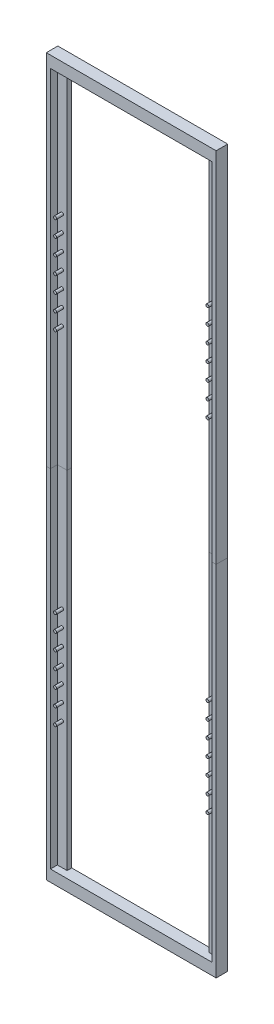
SolidWorks part; units mm, degrees
ref_plane "Front Plane" through (0, 0, 0) normal (1, 0, 0) x (0, 1, 0)
ref_plane "Top Plane" through (0, 0, 0) normal (0, 0, 1) x (0, 1, 0)
ref_plane "Right Plane" through (0, 0, 0) normal (0, 1, 0) x (-1, 0, 0)
sketch "Sketch1" plane through (0, 0, 0) normal (0, 0, 1) x (0, 1, 0)
  line L1 (-150, -30.75) -> (150, -30.75)
  line L2 (-150, -30.75) -> (-150, 30.75)
  line L3 (-150, 30.75) -> (150, 30.75)
  line L4 (150, -30.75) -> (150, 30.75)
  line L5 (-150, -30.75) -> (150, 30.75) construction
  line L6 (-150, 30.75) -> (150, -30.75) construction
  line L7 (-155, -36.75) -> (155, -36.75)
  line L8 (-155, -36.75) -> (-155, 36.75)
  line L9 (-155, 36.75) -> (155, 36.75)
  line L10 (155, -36.75) -> (155, 36.75)
  line L11 (-155, -36.75) -> (155, 36.75) construction
  line L12 (-155, 36.75) -> (155, -36.75) construction
  point P0 (0, 0)
  point P6 (0, 0)
  dimension "D1" = 61.5
  dimension "D2" = 6
  dimension "D3" = 300
  dimension "D4" = 310
extrude "Boss-Extrude1" add sketch "Sketch1" along normal blind 5
sketch "Sketch2" plane through (0, 0, 5) normal (0, 0, 1) x (1, 0, 0)
  line L1 (-30.75, 150) -> (-34.95, 150)
  line L2 (-30.75, 150) -> (-30.75, -150)
  line L3 (-30.75, -150) -> (-34.95, -150)
  line L4 (-34.95, 150) -> (-34.95, -150)
  line L5 (30.75, -150) -> (34.95, -150)
  line L6 (30.75, -150) -> (30.75, 150)
  line L7 (30.75, 150) -> (34.95, 150)
  line L8 (34.95, -150) -> (34.95, 150)
  dimension "D1" = 4.2
  dimension "D2" = 4.2
ref_plane "Plane1" through (-36.75, 155, 5) normal (0, -1, 0) x (-1, 0, 0)
extrude "Cut-Extrude1" cut sketch "Sketch2" against normal blind 3 contours L4 L3 L2 L1 | L8 L7 L6 L5
sketch "Sketch6" plane through (0, 0, 2) normal (0, 0, 1) x (1, 0, 0)
  line L4 (30.75, -150) -> (34.95, -150)
  line L5 (34.95, -150) -> (34.95, 150)
  line L6 (34.95, 150) -> (30.75, 150)
  line L7 (30.75, 150) -> (30.75, -150)
  line L8 (30.75, -150) -> (34.95, -150)
  line L9 (34.95, -150) -> (34.95, 150)
  line L10 (34.95, 150) -> (30.75, 150)
  line L11 (30.75, 150) -> (30.75, -150)
  dimension "D1" = 0
sketch "Sketch7" plane through (0, 0, 2) normal (0, 0, 1) x (1, 0, 0)
  line L0 (-31.65, 55) -> (-33.25, 55) construction
  line L1 (-34.45, 53.8) -> (-34.45, 52.2) construction
  line L2 (-33.25, 51) -> (-31.65, 51) construction
  line L3 (-30.45, 49.8) -> (-30.45, 56.2) construction
  line L4 (34.45, 66.2) -> (34.45, 67.8)
  line L5 (33.25, 69) -> (31.65, 69)
  line L6 (30.45, 70.2) -> (30.45, 63.8)
  line L7 (31.65, 65) -> (33.25, 65)
  line L8 (34.45, 66.2) -> (34.45, 67.8)
  line L9 (33.25, 69) -> (31.65, 69)
  line L10 (30.45, 70.2) -> (30.45, 63.8)
  line L11 (31.65, 65) -> (33.25, 65)
  line L12 (-31.65, 69) -> (-33.25, 69) construction
  line L13 (-34.45, 67.8) -> (-34.45, 66.2) construction
  line L14 (-33.25, 65) -> (-31.65, 65) construction
  line L15 (-30.45, 63.8) -> (-30.45, 70.2) construction
  line L16 (-31.65, -51) -> (-33.25, -51) construction
  line L17 (-34.45, -52.2) -> (-34.45, -53.8) construction
  line L18 (-33.25, -55) -> (-31.65, -55) construction
  line L19 (-30.45, -56.2) -> (-30.45, -49.8) construction
  line L20 (-31.65, -65) -> (-33.25, -65) construction
  line L21 (-34.45, -66.2) -> (-34.45, -67.8) construction
  line L22 (-33.25, -69) -> (-31.65, -69) construction
  line L23 (-30.45, -70.2) -> (-30.45, -63.8) construction
  line L24 (31.65, -69) -> (33.25, -69) construction
  line L25 (34.45, -67.8) -> (34.45, -66.2) construction
  line L26 (33.25, -65) -> (31.65, -65) construction
  line L27 (30.45, -63.8) -> (30.45, -70.2) construction
  line L28 (34.45, -53.8) -> (34.45, -52.2) construction
  line L29 (33.25, -51) -> (31.65, -51) construction
  line L30 (30.45, -49.8) -> (30.45, -56.2) construction
  line L31 (31.65, -55) -> (33.25, -55) construction
  line L32 (31.65, 51) -> (33.25, 51) construction
  line L33 (34.45, 52.2) -> (34.45, 53.8) construction
  line L34 (33.25, 55) -> (31.65, 55) construction
  line L35 (30.45, 56.2) -> (30.45, 49.8) construction
  line L36 (-31.65, 55) -> (-33.25, 55)
  line L37 (-34.45, 53.8) -> (-34.45, 52.2)
  line L38 (-33.25, 51) -> (-31.65, 51)
  line L39 (-30.45, 49.8) -> (-30.45, 56.2)
  line L40 (-31.65, 69) -> (-33.25, 69)
  line L41 (-34.45, 67.8) -> (-34.45, 66.2)
  line L42 (-33.25, 65) -> (-31.65, 65)
  line L43 (-30.45, 63.8) -> (-30.45, 70.2)
  line L44 (-31.65, -51) -> (-33.25, -51)
  line L45 (-34.45, -52.2) -> (-34.45, -53.8)
  line L46 (-33.25, -55) -> (-31.65, -55)
  line L47 (-30.45, -56.2) -> (-30.45, -49.8)
  line L48 (-31.65, -65) -> (-33.25, -65)
  line L49 (-34.45, -66.2) -> (-34.45, -67.8)
  line L50 (-33.25, -69) -> (-31.65, -69)
  line L51 (-30.45, -70.2) -> (-30.45, -63.8)
  line L52 (31.65, -69) -> (33.25, -69)
  line L53 (34.45, -67.8) -> (34.45, -66.2)
  line L54 (33.25, -65) -> (31.65, -65)
  line L55 (30.45, -63.8) -> (30.45, -70.2)
  line L56 (34.45, -53.8) -> (34.45, -52.2)
  line L57 (33.25, -51) -> (31.65, -51)
  line L58 (30.45, -49.8) -> (30.45, -56.2)
  line L59 (31.65, -55) -> (33.25, -55)
  line L60 (31.65, 51) -> (33.25, 51)
  line L61 (34.45, 52.2) -> (34.45, 53.8)
  line L62 (33.25, 55) -> (31.65, 55)
  line L63 (30.45, 56.2) -> (30.45, 49.8)
  arc A0 (-33.25, 55) -> (-34.45, 53.8) centre (-33.25, 53.8) ccw construction
  circle A1 centre (32.95, 67) radius 0.75
  circle A2 centre (32.95, 67) radius 0.75
  arc A3 (-34.45, 52.2) -> (-33.25, 51) centre (-33.25, 52.2) ccw construction
  arc A4 (-30.45, 49.8) -> (-31.65, 51) centre (-31.65, 49.8) ccw construction
  arc A5 (-31.65, 55) -> (-30.45, 56.2) centre (-31.65, 56.2) ccw construction
  arc A6 (34.45, 67.8) -> (33.25, 69) centre (33.25, 67.8) ccw
  arc A7 (30.45, 70.2) -> (31.65, 69) centre (31.65, 70.2) ccw
  arc A8 (31.65, 65) -> (30.45, 63.8) centre (31.65, 63.8) ccw
  arc A9 (33.25, 65) -> (34.45, 66.2) centre (33.25, 66.2) ccw
  arc A10 (34.45, 67.8) -> (33.25, 69) centre (33.25, 67.8) ccw
  arc A11 (30.45, 70.2) -> (31.65, 69) centre (31.65, 70.2) ccw
  arc A12 (31.65, 65) -> (30.45, 63.8) centre (31.65, 63.8) ccw
  arc A13 (33.25, 65) -> (34.45, 66.2) centre (33.25, 66.2) ccw
  arc A14 (-33.25, 69) -> (-34.45, 67.8) centre (-33.25, 67.8) ccw construction
  arc A15 (-34.45, 66.2) -> (-33.25, 65) centre (-33.25, 66.2) ccw construction
  arc A16 (-30.45, 63.8) -> (-31.65, 65) centre (-31.65, 63.8) ccw construction
  arc A17 (-31.65, 69) -> (-30.45, 70.2) centre (-31.65, 70.2) ccw construction
  arc A18 (-33.25, -51) -> (-34.45, -52.2) centre (-33.25, -52.2) ccw construction
  arc A19 (-34.45, -53.8) -> (-33.25, -55) centre (-33.25, -53.8) ccw construction
  arc A20 (-30.45, -56.2) -> (-31.65, -55) centre (-31.65, -56.2) ccw construction
  arc A21 (-31.65, -51) -> (-30.45, -49.8) centre (-31.65, -49.8) ccw construction
  arc A22 (-33.25, -65) -> (-34.45, -66.2) centre (-33.25, -66.2) ccw construction
  arc A23 (-34.45, -67.8) -> (-33.25, -69) centre (-33.25, -67.8) ccw construction
  arc A24 (-30.45, -70.2) -> (-31.65, -69) centre (-31.65, -70.2) ccw construction
  arc A25 (-31.65, -65) -> (-30.45, -63.8) centre (-31.65, -63.8) ccw construction
  arc A26 (33.25, -69) -> (34.45, -67.8) centre (33.25, -67.8) ccw construction
  arc A27 (34.45, -66.2) -> (33.25, -65) centre (33.25, -66.2) ccw construction
  arc A28 (30.45, -63.8) -> (31.65, -65) centre (31.65, -63.8) ccw construction
  arc A29 (31.65, -69) -> (30.45, -70.2) centre (31.65, -70.2) ccw construction
  arc A30 (34.45, -52.2) -> (33.25, -51) centre (33.25, -52.2) ccw construction
  arc A31 (30.45, -49.8) -> (31.65, -51) centre (31.65, -49.8) ccw construction
  arc A32 (31.65, -55) -> (30.45, -56.2) centre (31.65, -56.2) ccw construction
  arc A33 (33.25, -55) -> (34.45, -53.8) centre (33.25, -53.8) ccw construction
  arc A34 (33.25, 51) -> (34.45, 52.2) centre (33.25, 52.2) ccw construction
  arc A35 (34.45, 53.8) -> (33.25, 55) centre (33.25, 53.8) ccw construction
  arc A36 (30.45, 56.2) -> (31.65, 55) centre (31.65, 56.2) ccw construction
  arc A37 (31.65, 51) -> (30.45, 49.8) centre (31.65, 49.8) ccw construction
  arc A38 (-33.25, 55) -> (-34.45, 53.8) centre (-33.25, 53.8) ccw
  arc A39 (-34.45, 52.2) -> (-33.25, 51) centre (-33.25, 52.2) ccw
  arc A40 (-30.45, 49.8) -> (-31.65, 51) centre (-31.65, 49.8) ccw
  arc A41 (-31.65, 55) -> (-30.45, 56.2) centre (-31.65, 56.2) ccw
  arc A42 (-33.25, 69) -> (-34.45, 67.8) centre (-33.25, 67.8) ccw
  arc A43 (-34.45, 66.2) -> (-33.25, 65) centre (-33.25, 66.2) ccw
  arc A44 (-30.45, 63.8) -> (-31.65, 65) centre (-31.65, 63.8) ccw
  arc A45 (-31.65, 69) -> (-30.45, 70.2) centre (-31.65, 70.2) ccw
  arc A46 (-33.25, -51) -> (-34.45, -52.2) centre (-33.25, -52.2) ccw
  arc A47 (-34.45, -53.8) -> (-33.25, -55) centre (-33.25, -53.8) ccw
  arc A48 (-30.45, -56.2) -> (-31.65, -55) centre (-31.65, -56.2) ccw
  arc A49 (-31.65, -51) -> (-30.45, -49.8) centre (-31.65, -49.8) ccw
  arc A50 (-33.25, -65) -> (-34.45, -66.2) centre (-33.25, -66.2) ccw
  arc A51 (-34.45, -67.8) -> (-33.25, -69) centre (-33.25, -67.8) ccw
  arc A52 (-30.45, -70.2) -> (-31.65, -69) centre (-31.65, -70.2) ccw
  arc A53 (-31.65, -65) -> (-30.45, -63.8) centre (-31.65, -63.8) ccw
  arc A54 (33.25, -69) -> (34.45, -67.8) centre (33.25, -67.8) ccw
  arc A55 (34.45, -66.2) -> (33.25, -65) centre (33.25, -66.2) ccw
  arc A56 (30.45, -63.8) -> (31.65, -65) centre (31.65, -63.8) ccw
  arc A57 (31.65, -69) -> (30.45, -70.2) centre (31.65, -70.2) ccw
  arc A58 (34.45, -52.2) -> (33.25, -51) centre (33.25, -52.2) ccw
  arc A59 (30.45, -49.8) -> (31.65, -51) centre (31.65, -49.8) ccw
  arc A60 (31.65, -55) -> (30.45, -56.2) centre (31.65, -56.2) ccw
  arc A61 (33.25, -55) -> (34.45, -53.8) centre (33.25, -53.8) ccw
  arc A62 (33.25, 51) -> (34.45, 52.2) centre (33.25, 52.2) ccw
  arc A63 (34.45, 53.8) -> (33.25, 55) centre (33.25, 53.8) ccw
  arc A64 (30.45, 56.2) -> (31.65, 55) centre (31.65, 56.2) ccw
  arc A65 (31.65, 51) -> (30.45, 49.8) centre (31.65, 49.8) ccw
  circle A66 centre (32.95, 53) radius 0.75 construction
  circle A67 centre (32.95, -53) radius 0.75 construction
  circle A68 centre (32.95, -67) radius 0.75 construction
  circle A69 centre (-32.95, -67) radius 0.75 construction
  circle A70 centre (-32.95, -53) radius 0.75 construction
  circle A71 centre (-32.95, 53) radius 0.75 construction
  circle A72 centre (-32.95, 67) radius 0.75 construction
  circle A73 centre (32.95, 53) radius 0.75
  circle A74 centre (32.95, -53) radius 0.75
  circle A75 centre (32.95, -67) radius 0.75
  circle A76 centre (-32.95, -67) radius 0.75
  circle A77 centre (-32.95, -53) radius 0.75
  circle A78 centre (-32.95, 53) radius 0.75
  circle A79 centre (-32.95, 67) radius 0.75
  circle A80 centre (-32.95, -67) radius 0.65
  circle A81 centre (-32.95, -53) radius 0.65
  circle A82 centre (-32.95, 53) radius 0.65
  circle A83 centre (-32.95, 67) radius 0.65
  circle A84 centre (32.95, 67) radius 0.65
  circle A85 centre (32.95, 53) radius 0.65
  circle A86 centre (32.95, -53) radius 0.65
  circle A87 centre (32.95, -67) radius 0.65
  circle A88 centre (32.95, -60) radius 0.65
  circle A89 centre (32.95, -74) radius 0.65
  circle A90 centre (32.95, -67) radius 0.65
  circle A91 centre (32.95, -81) radius 0.65
  circle A92 centre (32.95, -74) radius 0.65
  circle A93 centre (32.95, -88) radius 0.65
  circle A94 centre (32.95, -81) radius 0.65
  circle A95 centre (32.95, -95) radius 0.65
  circle A96 centre (-32.95, -74) radius 0.65
  circle A97 centre (-32.95, -60) radius 0.65
  circle A98 centre (-32.95, -81) radius 0.65
  circle A99 centre (-32.95, -67) radius 0.65
  circle A100 centre (-32.95, -88) radius 0.65
  circle A101 centre (-32.95, -74) radius 0.65
  circle A102 centre (-32.95, -95) radius 0.65
  circle A103 centre (-32.95, -81) radius 0.65
  circle A104 centre (-32.95, 74) radius 0.65
  circle A105 centre (-32.95, 60) radius 0.65
  circle A106 centre (-32.95, 81) radius 0.65
  circle A107 centre (-32.95, 67) radius 0.65
  circle A108 centre (-32.95, 88) radius 0.65
  circle A109 centre (-32.95, 74) radius 0.65
  circle A110 centre (-32.95, 95) radius 0.65
  circle A111 centre (-32.95, 81) radius 0.65
  circle A112 centre (32.95, 60) radius 0.65
  circle A113 centre (32.95, 74) radius 0.65
  circle A114 centre (32.95, 67) radius 0.65
  circle A115 centre (32.95, 81) radius 0.65
  circle A116 centre (32.95, 74) radius 0.65
  circle A117 centre (32.95, 88) radius 0.65
  circle A118 centre (32.95, 81) radius 0.65
  circle A119 centre (32.95, 95) radius 0.65
  dimension "D3" = 0.1
  dimension "D4" = 0.1
  dimension "D5" = 0.1
  dimension "D6" = 0.1
  dimension "D7" = 0.1
  dimension "D8" = 0.1
  dimension "D9" = 0.1
  dimension "D10" = 0.1
  dimension "D1" = 0
  dimension "D2" = 0
  dimension "D11" = 5
  dimension "D12" = 5
  dimension "D13" = 5
  dimension "D14" = 5
sketch "Sketch8" plane through (0, 0, 2) normal (0, 0, 1) x (1, 0, 0)
  line L0 (34.95, 150) -> (30.75, 150) construction
  circle A0 centre (32.95, 67) radius 0.55
  circle A1 centre (32.95, 53) radius 0.55
  circle A2 centre (32.95, 53) radius 0.75 construction
  circle A3 centre (32.95, 67) radius 0.75 construction
  circle A6 centre (32.95, 60) radius 0.55
  circle A7 centre (32.95, 74) radius 0.55
  circle A8 centre (32.95, 67) radius 0.55
  circle A9 centre (32.95, 81) radius 0.55
  circle A10 centre (32.95, 74) radius 0.55
  circle A11 centre (32.95, 88) radius 0.55
  circle A12 centre (32.95, 81) radius 0.55
  circle A13 centre (32.95, 95) radius 0.55
  point P13 (32.95, 96.8)
  dimension "D1" = 0.2
  dimension "D2" = 0.2
  dimension "D3" = 53.2
  dimension "D4" = 5
extrude "Boss-Extrude2" add sketch "Sketch7" along normal blind 3 contours A82 | A83 | A84 | A85 | A86 | A87 | A81 | A88 | A89 | A91 | A93 | A80 | A95 | A97 | A96 | A98 | A100 | A105 | A104 | A106 | A108 | A102 | A110 | A119 | A117 | A115 | A113 | A112
ref_plane "Plane2" through (0, 0, 0) normal (0, -1, 0) x (-1, 0, 0)
split "Split1" trim tools "Plane2" bodies to split 103 resulting bodies 113 114
sketch "Sketch18" plane through (36.75, 0, 0) normal (1, 0, 0) x (0, 1, 0)
  line L0 (-155, 5) -> (0, 5) construction
  line L1 (0, 0) -> (-15, 0)
  line L2 (0, 0) -> (0, 5)
  line L3 (0, 5) -> (-15, 5)
  line L4 (-15, 0) -> (-15, 5)
  dimension "D1" = 15
sketch "Sketch19" plane through (36.75, 0, 0) normal (1, 0, 0) x (0, 1, 0)
  line L0 (0, 0) -> (155, 0) construction
  line L1 (0, 5) -> (15, 5)
  line L2 (0, 5) -> (0, 0)
  line L3 (0, 0) -> (15, 0)
  line L4 (15, 5) -> (15, 0)
  dimension "D1" = 15
